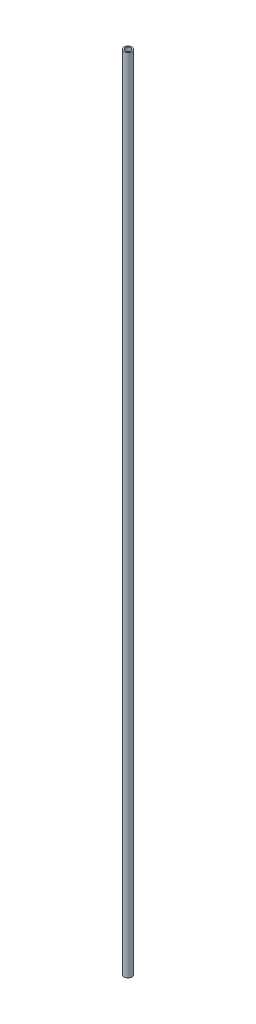
SolidWorks part; units mm, degrees
ref_plane "Alzado" through (0, 0, 0) normal (0, 0, 1) x (1, 0, 0)
ref_plane "Planta" through (0, 0, 0) normal (0, 1, 0) x (1, 0, 0)
ref_plane "Vista lateral" through (0, 0, 0) normal (1, 0, 0) x (0, 0, -1)
sketch "Croquis1" plane through (0, 0, 0) normal (0, 0, 1) x (1, 0, 0)
  line L0 (0, 37.2593) -> (0, -30.5297) construction
  line L1 (3.16, 34.1407) -> (4.76, 34.1407)
  line L4 (4.76, 34.1407) -> (4.76, -905.8593)
  line L5 (4.76, -905.8593) -> (3.76, -905.8593)
  line L6 (3.76, -905.8593) -> (3.76, -897.8593)
  line L7 (3.76, -897.8593) -> (3.16, -897.8593)
  line L8 (3.16, -897.8593) -> (3.16, 34.1407)
  dimension "D1" = 4.76
  dimension "D4" = 1.6
  dimension "D5" = 1
  dimension "D6" = 8
revolve "Revolución1" add sketch "Croquis1" angle 360 about L0
